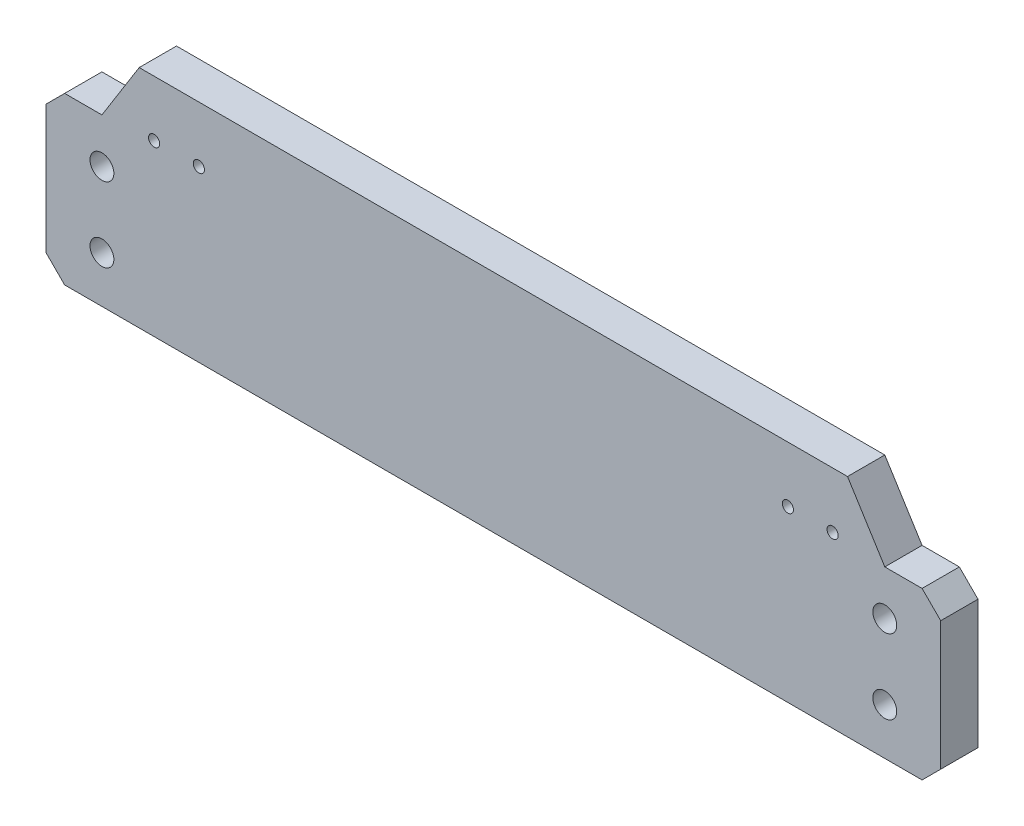
SolidWorks part; units mm, degrees
material "Pine"
ref_plane "Front Plane" through (0, 0, 0) normal (0, 0, 1) x (1, 0, 0)
ref_plane "Top Plane" through (0, 0, 0) normal (0, 1, 0) x (1, 0, 0)
ref_plane "Right Plane" through (0, 0, 0) normal (1, 0, 0) x (0, 0, -1)
sketch "Sketch1" plane through (0, 0, 0) normal (0, 0, 1) x (1, 0, 0)
  line L0 (-115, -7.75) -> (-95, -7.75) construction
  line L1 (-120, -30.25) -> (120, -30.25)
  line L2 (-120, -30.25) -> (-120, 30.25)
  line L3 (-120, 30.25) -> (120, 30.25)
  line L4 (120, -30.25) -> (120, 30.25)
  line L5 (-120, -30.25) -> (120, 30.25) construction
  line L6 (-120, 30.25) -> (120, -30.25) construction
  line L7 (-115, 12.25) -> (-95, 12.25) construction
  line L8 (-115, 12.25) -> (-115, -27.75) construction
  line L9 (-115, -27.75) -> (-95, -27.75) construction
  line L10 (-95, 12.25) -> (-95, -27.75) construction
  line L11 (-105, 12.25) -> (-105, -27.75) construction
  line L12 (0, 30.25) -> (0, -30.25) construction
  line L13 (105, 12.25) -> (105, -27.75) construction
  line L14 (95, 12.25) -> (95, -27.75) construction
  line L15 (115, -27.75) -> (95, -27.75) construction
  line L16 (115, 12.25) -> (115, -27.75) construction
  line L17 (115, 12.25) -> (95, 12.25) construction
  line L18 (115, -7.75) -> (95, -7.75) construction
  line L19 (-85, 20.25) -> (-85, 12.25) construction
  line L20 (-100, 12.25) -> (-70, 12.25) construction
  line L21 (-100, 12.25) -> (-100, 20.25) construction
  line L22 (-100, 20.25) -> (-70, 20.25) construction
  line L23 (-70, 12.25) -> (-70, 20.25) construction
  line L24 (70, 12.25) -> (70, 20.25) construction
  line L25 (100, 20.25) -> (70, 20.25) construction
  line L26 (100, 12.25) -> (100, 20.25) construction
  line L27 (100, 12.25) -> (70, 12.25) construction
  line L28 (85, 20.25) -> (85, 12.25) construction
  circle A0 centre (-105, 2.25) radius 3.2
  circle A1 centre (-105, -17.75) radius 3.2
  circle A2 centre (105, -17.75) radius 3.2
  circle A3 centre (105, 2.25) radius 3.2
  circle A4 centre (-91, 15.25) radius 1.5
  circle A5 centre (-79, 15.25) radius 1.5
  circle A6 centre (79, 15.25) radius 1.5
  circle A7 centre (91, 15.25) radius 1.5
  point P0 (0, 0)
  dimension "D2" = 40
  dimension "D4" = 20
  dimension "D5" = 6.4
  dimension "D9" = 12
  dimension "D14" = 3
  dimension "D1" = 30
  dimension "D3" = 20
  dimension "D6" = 2.5
  dimension "D7" = 210
  dimension "D8" = 5
  dimension "D10" = 3
  dimension "D11" = 8
  dimension "D12" = 170
  dimension "D13" = 10
extrude "Boss-Extrude1" add sketch "Sketch1" along normal blind 10
sketch "Sketch2" plane through (0, 0, 10) normal (0, 0, 1) x (1, 0, 0)
  line L0 (-120, 14.25) -> (-105, 14.25)
  line L1 (-120, 30.25) -> (-120, -30.25) construction
  line L2 (-105, 14.25) -> (-95, 30.25)
  line L3 (120, 30.25) -> (-120, 30.25) construction
  line L4 (0, 30.25) -> (0, -30.25) construction
  line L5 (-120, -30.25) -> (120, -30.25) construction
  line L6 (120, 30.25) -> (120, 14.25)
  line L7 (95, 30.25) -> (120, 30.25)
  line L8 (-95, 30.25) -> (-120, 30.25)
  line L9 (-120, 30.25) -> (-120, 14.25)
  line L10 (105, 14.25) -> (95, 30.25)
  line L11 (120, 14.25) -> (105, 14.25)
  dimension "D1" = 15
  dimension "D2" = 16
  dimension "D3" = 25
extrude "Cut-Extrude1" cut sketch "Sketch2" against normal through all
chamfer "Chamfer3" distance 5 angle 45 4 edges at (-120, 14.25, 5) (120, 14.25, 5) (120, -30.25, 5) (-120, -30.25, 5)
